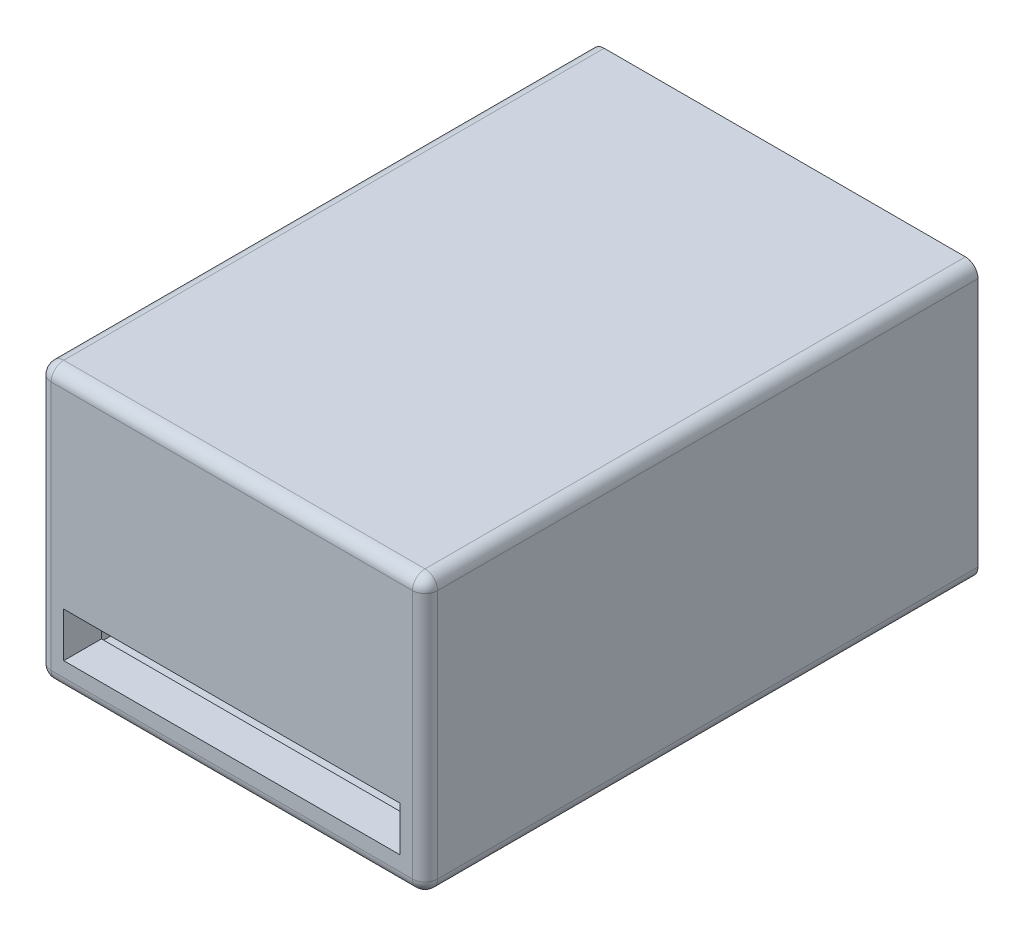
SolidWorks part; units mm, degrees
ref_plane "Plan de face" through (0, 0, 0) normal (0, 0, 1) x (1, 0, 0)
ref_plane "Plan de dessus" through (0, 0, 0) normal (0, 1, 0) x (1, 0, 0)
ref_plane "Plan de droite" through (0, 0, 0) normal (1, 0, 0) x (0, 0, -1)
sketch "Esquisse1" plane through (0, 0, 0) normal (0, 0, 1) x (1, 0, 0)
  line L1 (-31.6005, 34.6263) -> (29.8995, 34.6263)
  line L2 (-31.6005, 34.6263) -> (-31.6005, -9.1237)
  line L3 (-31.6005, -9.1237) -> (29.8995, -9.1237)
  line L4 (29.8995, 34.6263) -> (29.8995, -9.1237)
  dimension "D1" = 43.75
  dimension "D2" = 61.5
extrude "Boss.-Extru.1" add sketch "Esquisse1" along normal blind 88
sketch "Esquisse2" plane through (0, 34.6263, 0) normal (0, 1, 0) x (1, 0, 0)
  line L0 (29.8995, -88) -> (-31.6005, -88) construction
  line L1 (25.8995, -15) -> (-27.6005, -15)
  line L2 (25.8995, -15) -> (25.8995, -84)
  line L3 (25.8995, -84) -> (-27.6005, -84)
  line L4 (-27.6005, -15) -> (-27.6005, -84)
  line L5 (29.8995, -88) -> (29.8995, 0) construction
  dimension "D1" = 69
  dimension "D2" = 53.5
  dimension "D3" = 4
  dimension "D4" = 4
sketch "Esquisse3" plane through (0, 0, 88) normal (0, 0, 1) x (1, 0, 0)
  line L0 (-31.6005, -9.1237) -> (29.8995, -9.1237) construction
  line L1 (-27.6005, -5.1237) -> (25.8995, -5.1237)
  line L2 (-27.6005, -5.1237) -> (-27.6005, 30.6263)
  line L3 (-27.6005, 30.6263) -> (25.8995, 30.6263)
  line L4 (25.8995, -5.1237) -> (25.8995, 30.6263)
  line L5 (29.8995, -9.1237) -> (29.8995, 34.6263) construction
  line L6 (25.8995, -4.7816) -> (25.8995, 2.3366)
  line L15 (25.8995, 2.3366) -> (-27.6005, 2.3366)
  line L16 (-27.6005, 2.3366) -> (-27.6005, -4.7816)
  line L17 (-27.6005, -4.7816) -> (25.8995, -4.7816)
  dimension "D1" = 53.5
  dimension "D2" = 35.75
  dimension "D3" = 4
  dimension "D4" = 4
extrude "Enlèv. mat.-Extru.4" cut sketch "Esquisse3" against normal up to next
sketch "Esquisse6" plane through (0, 0, 0) normal (0, 0, -1) x (-1, 0, 0)
  line L7 (29.6005, 32.6263) -> (29.6005, -7.1237)
  line L8 (31.6005, 34.6263) -> (31.6005, -9.1237) construction
  line L10 (-29.8995, 34.6263) -> (31.6005, 34.6263) construction
  line L12 (31.6005, -9.1237) -> (-29.8995, -9.1237) construction
  line L13 (-27.9021, 32.6263) -> (29.6005, 32.6263)
  line L14 (-27.9021, 32.6263) -> (-27.9021, -7.1237)
  line L15 (-27.9021, -7.1237) -> (29.6005, -7.1237)
  line L18 (-29.8995, -9.1237) -> (-29.8995, 34.6263) construction
  dimension "D1" = 2
  dimension "D2" = 2
  dimension "D3" = 2
  dimension "D4" = 2
  dimension "D5" = 2
  dimension "D6" = 1.9974
  dimension "D7" = 2
extrude "Enlèv. mat.-Extru.5" cut sketch "Esquisse6" against normal blind 82
fillet "Congé4" radius 2 8 edges at (-31.6005, 34.6263, 44) (-31.6005, -9.1237, 44) (-31.6005, 12.7513, 88) (-0.8505, -9.1237, 88) (29.8995, -9.1237, 44) (29.8995, 12.7513, 88) (-0.8505, 34.6263, 88) (29.8995, 34.6263, 44)
sketch "Esquisse7" plane through (0, -7.1237, 0) normal (0, 1, 0) x (1, 0, 0)
  line L0 (27.9021, -82) -> (27.9021, 0) construction
  line L1 (27.9021, 0) -> (-29.6005, 0) construction
  circle A0 centre (18.0021, -9.4) radius 1.5
  point P4 (0, 0)
  point P5 (0, 0)
  dimension "D2" = 9.4
  dimension "D1" = 9.9
extrude "Boss.-Extru.2" add sketch "Esquisse7" along normal blind 5.2
sketch "Esquisse8" plane through (0, -7.1237, 0) normal (0, 1, 0) x (1, 0, 0)
  line L0 (-29.6005, -82) -> (-29.6005, 0) construction
  line L1 (27.9021, 0) -> (-29.6005, 0) construction
  circle A0 centre (-9.8505, -9.5) radius 1.5
  dimension "D1" = 19.75
  dimension "D2" = 9.5
extrude "Boss.-Extru.3" add sketch "Esquisse8" along normal blind 5.2
